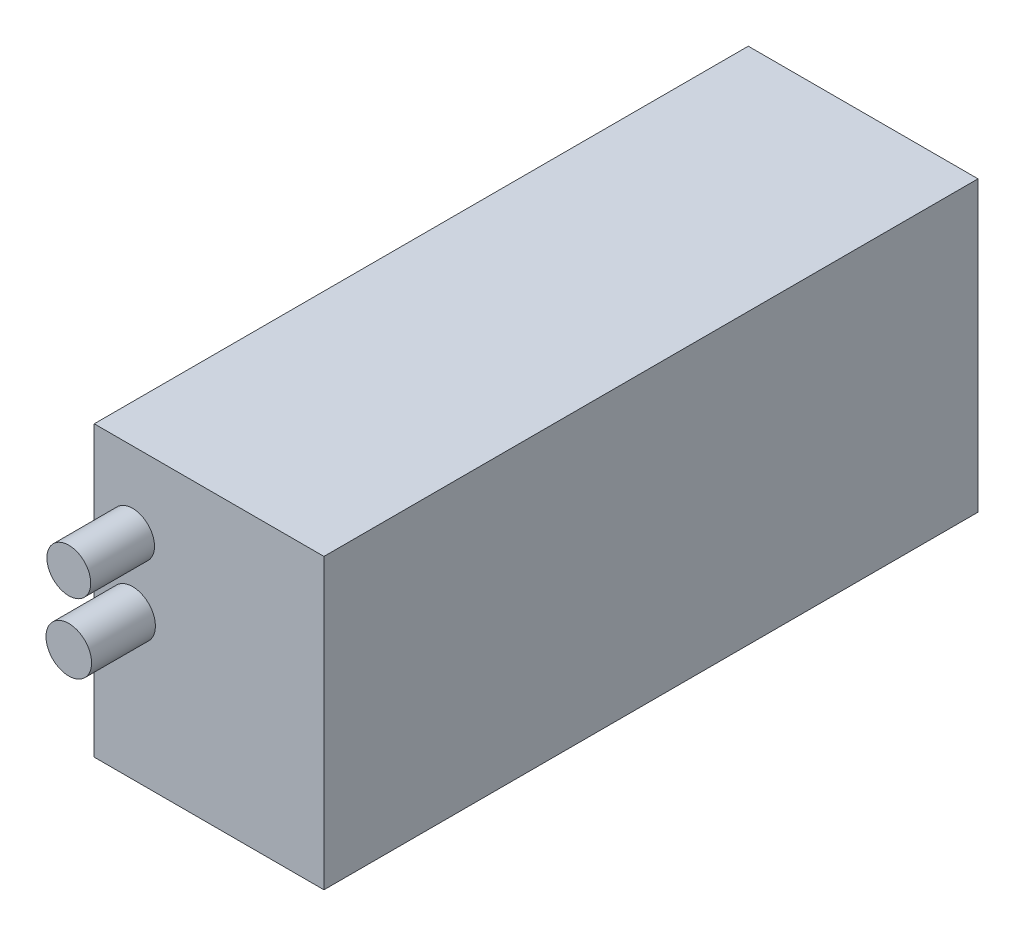
SolidWorks part; units mm, degrees
ref_plane "Front Plane" through (0, 0, 0) normal (0, 0, 1) x (1, 0, 0)
ref_plane "Top Plane" through (0, 0, 0) normal (0, 1, 0) x (1, 0, 0)
ref_plane "Right Plane" through (0, 0, 0) normal (1, 0, 0) x (0, 0, -1)
sketch "Sketch1" plane through (0, 0, 0) normal (0, 1, 0) x (1, 0, 0)
  line L1 (-36, -102.5) -> (36, -102.5)
  line L2 (-36, -102.5) -> (-36, 102.5)
  line L3 (-36, 102.5) -> (36, 102.5)
  line L4 (36, -102.5) -> (36, 102.5)
  line L5 (-36, -102.5) -> (36, 102.5) construction
  line L6 (-36, 102.5) -> (36, -102.5) construction
  point P0 (0, 0)
  dimension "D1" = 72
  dimension "D2" = 205
extrude "Boss-Extrude1" add sketch "Sketch1" along normal blind 90.5
sketch "Sketch3" plane through (0, 0, 102.5) normal (0, 0, 1) x (1, 0, 0)
  circle A0 centre (-23.9735, 66.6951) radius 6.8698
  circle A1 centre (-23.9735, 45.1761) radius 7.1458
extrude "Boss-Extrude2" add sketch "Sketch3" along normal blind 20
sketch "Sketch11" plane through (0, 90.5, 0) normal (0, 1, 0) x (1, 0, 0)
  line L0 (0, 102.5) -> (0, -102.5) construction
  line L2 (36, 102.5) -> (-36, 102.5) construction
  line L3 (-36, -102.5) -> (36, -102.5) construction
  text T0 "Luminier 22000mAh 6s Battery" font "Century Gothic" height 3.5
